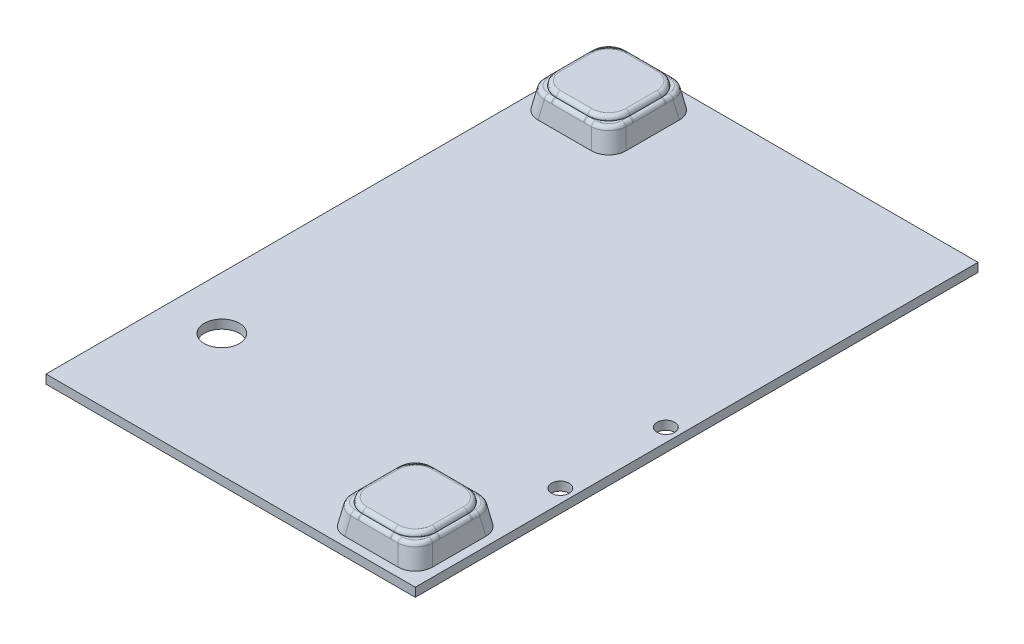
SolidWorks part; units mm, degrees
ref_plane "Front Plane" through (0, 0, 0) normal (0, 0, 1) x (1, 0, 0)
ref_plane "Top Plane" through (0, 0, 0) normal (0, 1, 0) x (1, 0, 0)
ref_plane "Right Plane" through (0, 0, 0) normal (1, 0, 0) x (0, 0, -1)
sketch "Sketch1" plane through (0, 0, 0) normal (0, 1, 0) x (1, 0, 0)
  line L1 (80.8254, -230.0534) -> (-78.1754, -230.0534)
  line L2 (80.8254, -230.0534) -> (80.8254, 107.5009)
  line L3 (80.8254, 107.5009) -> (-78.1754, 107.5009)
  line L4 (-78.1754, -230.0534) -> (-78.1754, 107.5009)
  line L5 (80.8254, -230.0534) -> (-78.1754, 107.5009) construction
  line L6 (80.8254, 107.5009) -> (-78.1754, -230.0534) construction
  point P1 (0, 0)
extrude "Boss-Extrude1" add sketch "Sketch1" along normal blind 6.35
sketch "Sketch2" plane through (0, 6.35, 0) normal (0, 1, 0) x (1, 0, 0)
  line L5 (1.325, 141.9237) -> (1.325, -230.0534) construction
  line L6 (-78.1754, -230.0534) -> (80.8254, -230.0534) construction
  line L7 (80.8254, 107.5009) -> (-78.1754, -230.0534) construction
  line L8 (134.675, -264.4763) -> (-132.025, -264.4763)
  line L9 (134.675, -264.4763) -> (134.675, 141.9237)
  line L10 (134.675, 141.9237) -> (-132.025, 141.9237)
  line L11 (-132.025, -264.4763) -> (-132.025, 141.9237)
  line L12 (134.675, -264.4763) -> (-132.025, 141.9237) construction
  line L13 (134.675, 141.9237) -> (-132.025, -264.4763) construction
  point P10 (1.325, -230.0534)
  point P11 (1.325, -61.2763)
  point P20 (1.325, -61.2763)
  dimension "D2" = 406.4
  dimension "D3" = 266.7
extrude "Boss-Extrude2" add sketch "Sketch2" against normal up to surface (6.35 mm away) up to face at (1.325, 0, 61.2763)
sketch "Sketch3" plane through (0, 6.35, 0) normal (0, 1, 0) x (1, 0, 0)
  line L0 (-132.025, -264.4763) -> (134.675, -264.4763) construction
  line L1 (-132.025, 141.9237) -> (-132.025, -264.4763) construction
  circle A0 centre (-93.925, -175.5763) radius 12.7
  dimension "D1" = 88.9
  dimension "D3" = 25.4
  dimension "D2" = 38.1
extrude "Cut-Extrude1" cut sketch "Sketch3" against normal blind 10
sketch "Sketch4" plane through (0, 6.35, 0) normal (0, 1, 0) x (1, 0, 0)
  circle A1 centre (125.15, -150.1763) radius 6.35
  circle A2 centre (125.15, -150.1763) radius 6.35
  circle A3 centre (125.15, -73.9763) radius 6.35
  circle A4 centre (125.15, -73.9763) radius 6.35
  dimension "D1" = 0
  dimension "D2" = 0
extrude "Cut-Extrude2" cut sketch "Sketch4" against normal blind 12.7
sketch "Sketch5" plane through (0, 6.35, 0) normal (0, 1, 0) x (1, 0, 0)
  line L0 (-93.925, 103.8237) -> (-132.025, 103.8237) construction
  line L1 (128.325, -258.1263) -> (64.825, -258.1263)
  line L2 (128.325, -258.1263) -> (128.325, -194.6263)
  line L3 (128.325, -194.6263) -> (64.825, -194.6263)
  line L4 (64.825, -258.1263) -> (64.825, -194.6263)
  line L5 (128.325, -258.1263) -> (64.825, -194.6263) construction
  line L6 (128.325, -194.6263) -> (64.825, -258.1263) construction
  line L7 (-62.175, 72.0737) -> (-125.675, 72.0737)
  line L8 (-62.175, 72.0737) -> (-62.175, 135.5737)
  line L9 (-62.175, 135.5737) -> (-125.675, 135.5737)
  line L10 (-125.675, 72.0737) -> (-125.675, 135.5737)
  line L11 (-62.175, 72.0737) -> (-125.675, 135.5737) construction
  line L12 (-62.175, 135.5737) -> (-125.675, 72.0737) construction
  line L13 (-132.025, 141.9237) -> (-132.025, -264.4763) construction
  line L14 (-93.925, 103.8237) -> (-93.925, 141.9237) construction
  line L15 (134.675, 141.9237) -> (-132.025, 141.9237) construction
  line L16 (96.575, -226.3763) -> (96.575, -264.4763) construction
  line L17 (-132.025, -264.4763) -> (134.675, -264.4763) construction
  line L18 (96.575, -226.3763) -> (134.675, -226.3763) construction
  line L19 (134.675, -264.4763) -> (134.675, 141.9237) construction
  point P0 (96.575, -226.3763)
  point P5 (-93.925, 103.8237)
  dimension "D1" = 63.5
  dimension "D2" = 38.1
extrude "Boss-Extrude3" add sketch "Sketch5" along normal blind 15.24 draft 10
sketch "Sketch6" plane through (0, 21.59, 0) normal (0, 1, 0) x (1, 0, 0)
  line L0 (125.6378, -255.439) -> (67.5122, -197.3135) construction
  line L1 (-67.4022, 77.301) -> (-120.4478, 77.301)
  line L2 (-67.4022, 77.301) -> (-67.4022, 130.3465)
  line L3 (-67.4022, 130.3465) -> (-120.4478, 130.3465)
  line L4 (-120.4478, 77.301) -> (-120.4478, 130.3465)
  line L5 (-67.4022, 77.301) -> (-120.4478, 130.3465) construction
  line L6 (-67.4022, 130.3465) -> (-120.4478, 77.301) construction
  line L7 (123.0978, -252.899) -> (70.0522, -252.899)
  line L8 (123.0978, -252.899) -> (123.0978, -199.8535)
  line L9 (123.0978, -199.8535) -> (70.0522, -199.8535)
  line L10 (70.0522, -252.899) -> (70.0522, -199.8535)
  line L11 (123.0978, -252.899) -> (70.0522, -199.8535) construction
  line L12 (123.0978, -199.8535) -> (70.0522, -252.899) construction
  line L13 (125.6378, -197.3135) -> (67.5122, -197.3135) construction
  line L14 (-122.9878, 132.8865) -> (-64.8622, 74.761) construction
  line L15 (-122.9878, 132.8865) -> (-122.9878, 74.761) construction
  line L16 (-64.8622, 132.8865) -> (-122.9878, 132.8865) construction
  line L17 (-64.8622, 74.761) -> (-64.8622, 132.8865) construction
  point P0 (-93.925, 103.8237)
  point P5 (96.575, -226.3763)
  point P31 (-93.925, 103.8237)
  dimension "D1" = 2.54
extrude "Boss-Extrude4" add sketch "Sketch6" along normal blind 3.048 draft 5
fillet "Fillet1" radius 15.24 8 edges at (122.9644, 23.114, 199.9868) (70.1856, 23.114, 199.9868) (122.9644, 23.114, 252.7657) (70.1856, 23.114, 252.7657) (-67.5356, 23.114, -77.4343) (-120.3144, 23.114, -77.4343) (-67.5356, 23.114, -130.2132) (-120.3144, 23.114, -130.2132)
fillet "Fillet2" radius 12.7 8 edges at (-63.5186, 13.97, -134.2301) (-63.5186, 13.97, -73.4173) (-124.3314, 13.97, -73.4173) (-124.3314, 13.97, -134.2301) (66.1686, 13.97, 195.9699) (126.9814, 13.97, 195.9699) (126.9814, 13.97, 256.7827) (66.1686, 13.97, 256.7827)
fillet "Fillet3" radius 3.048 16 edges at (125.6378, 21.59, 226.3763) (121.9971, 21.59, 251.7984) (96.575, 21.59, 255.439) (71.1529, 21.59, 251.7984) (67.5122, 21.59, 226.3763) (71.1529, 21.59, 200.9542) (96.575, 21.59, 197.3135) (-64.8622, 21.59, -103.8237) (-68.5029, 21.59, -78.4016) (-93.925, 21.59, -74.761) (-119.3471, 21.59, -78.4016) (-122.9878, 21.59, -103.8237) (-119.3471, 21.59, -129.2458) (-93.925, 21.59, -132.8865) (121.9971, 21.59, 200.9542) (-68.5029, 21.59, -129.2458)
fillet "Fillet4" radius 3.048 16 edges at (-115.7414, 24.638, -82.0074) (-120.1811, 24.638, -103.8237) (-115.7414, 24.638, -125.6401) (-93.925, 24.638, -130.0798) (-72.1086, 24.638, -125.6401) (-67.6689, 24.638, -103.8237) (-72.1086, 24.638, -82.0074) (122.8311, 24.638, 226.3763) (118.3914, 24.638, 248.1926) (96.575, 24.638, 252.6324) (74.7586, 24.638, 248.1926) (70.3189, 24.638, 226.3763) (74.7586, 24.638, 204.5599) (96.575, 24.638, 200.1202) (-93.925, 24.638, -77.5676) (118.3914, 24.638, 204.5599)
sketch "Sketch9" plane through (0, 0, 0) normal (0, -1, 0) x (1, 0, 0)
  circle A1 centre (80.8254, 230.0534) radius 4.7625
  circle A2 centre (80.8254, 230.0534) radius 4.7625
  circle A3 centre (80.8254, -107.5009) radius 4.7625
  circle A4 centre (80.8254, -107.5009) radius 4.7625
  circle A5 centre (-78.1754, -107.5009) radius 4.7625
  circle A6 centre (-78.1754, -107.5009) radius 4.7625
  circle A7 centre (-78.1754, 230.0534) radius 4.7625
  circle A8 centre (-78.1754, 230.0534) radius 4.7625
  dimension "D1" = 0
  dimension "D2" = 0
  dimension "D3" = 0
  dimension "D4" = 0
